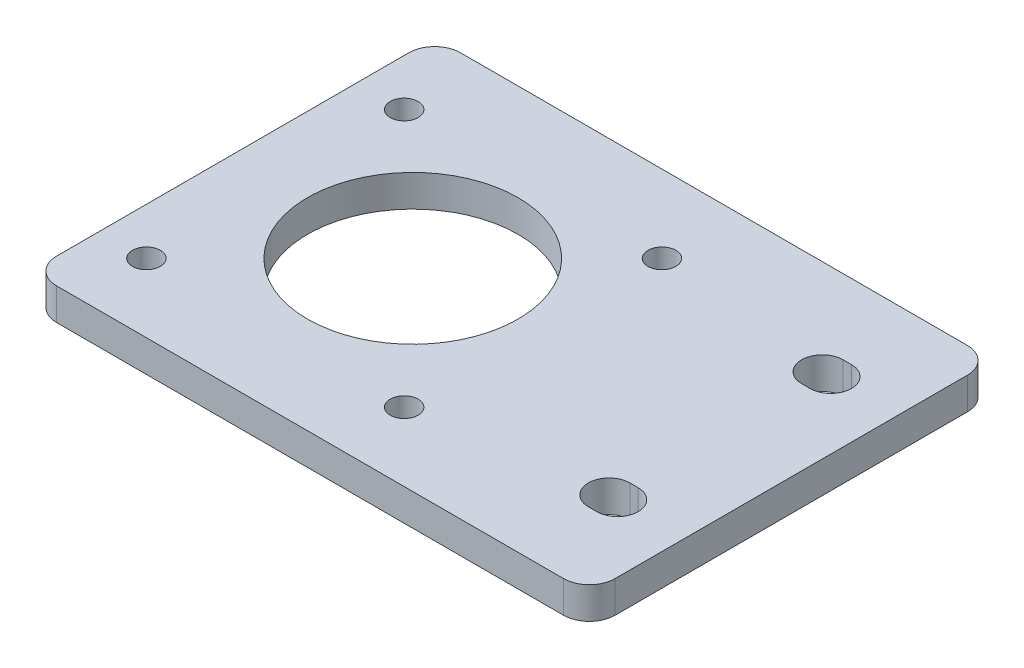
SolidWorks part; units mm, degrees
material "1060 Alloy"
ref_plane "Front Plane" through (0, 0, 0) normal (0, 0, 1) x (1, 0, 0)
ref_plane "Top Plane" through (0, 0, 0) normal (0, 1, 0) x (1, 0, 0)
ref_plane "Right Plane" through (0, 0, 0) normal (1, 0, 0) x (0, 0, -1)
sketch "Sketch1" plane through (0, 0, 0) normal (0, 1, 0) x (1, 0, 0)
  line L0 (-16.853, 10.7776) -> (51.4975, 10.7776) construction
  line L1 (-16.853, -12.7224) -> (48.147, -12.7224)
  line L2 (-16.853, -12.7224) -> (-16.853, 34.2776)
  line L3 (-16.853, 34.2776) -> (48.147, 34.2776)
  line L4 (48.147, -12.7224) -> (48.147, 34.2776)
  line L5 (39.357, -1.6324) -> (40.337, -1.6324) construction
  line L6 (39.357, 0.7776) -> (40.337, 0.7776)
  line L7 (39.357, -4.0424) -> (40.337, -4.0424)
  line L8 (39.357, 23.1876) -> (40.337, 23.1876) construction
  line L9 (39.357, 20.7776) -> (40.337, 20.7776)
  line L10 (39.357, 25.5976) -> (40.337, 25.5976)
  circle A0 centre (4.097, 10.7776) radius 12.25
  circle A1 centre (-11.403, -4.7224) radius 1.6238
  circle A2 centre (18.597, -4.7224) radius 1.6238
  circle A3 centre (18.597, 25.2776) radius 1.6238
  circle A4 centre (-11.403, 25.2776) radius 1.6238
  arc A5 (39.357, 0.7776) -> (39.357, -4.0424) centre (39.357, -1.6324) ccw
  arc A6 (40.337, -4.0424) -> (40.337, 0.7776) centre (40.337, -1.6324) ccw
  arc A7 (39.357, 20.7776) -> (39.357, 25.5976) centre (39.357, 23.1876) cw
  arc A8 (40.337, 25.5976) -> (40.337, 20.7776) centre (40.337, 23.1876) cw
  point P10 (39.847, -1.6324)
  point P23 (36.947, -1.6324)
  point P24 (42.747, -1.6324)
  point P28 (39.847, 23.1876)
  dimension "D3" = 24.5
  dimension "D1" = 65
  dimension "D2" = 47
  dimension "D4" = 20.95
  dimension "D5" = 15.5
  dimension "D6" = 15.5
  dimension "D9" = 4.82
  dimension "D10" = 5.8
  dimension "D11" = 5.4
  dimension "D12" = 20
  dimension "D7" = 2
  dimension "D8" = 2
extrude "Boss-Extrude1" add sketch "Sketch1" along normal blind 3.7
fillet "Fillet1" radius 3 4 edges at (-16.853, 1.85, -34.2776) (48.147, 1.85, -34.2776) (-16.853, 1.85, 12.7224) (48.147, 1.85, 12.7224)
